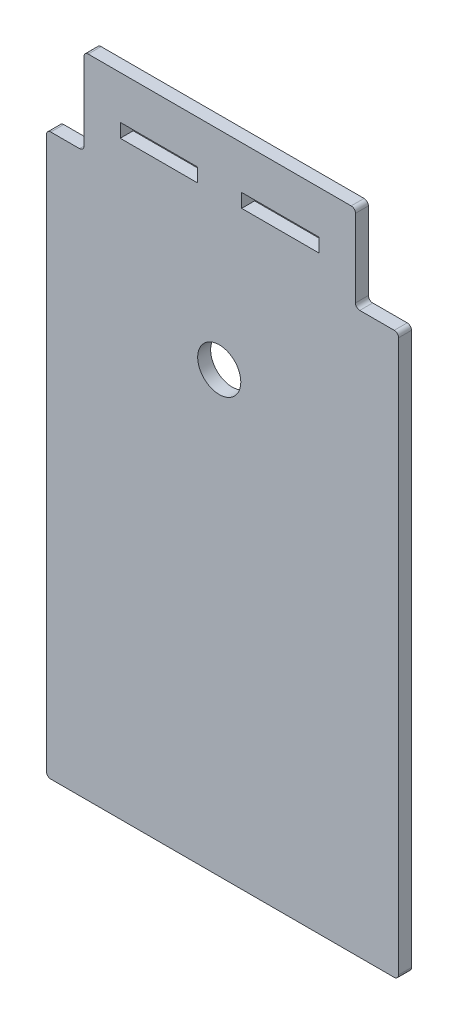
SolidWorks part; units mm, degrees
ref_plane "Alzado" through (0, 0, 0) normal (0, 0, 1) x (1, 0, 0)
ref_plane "Planta" through (0, 0, 0) normal (0, 1, 0) x (1, 0, 0)
ref_plane "Vista lateral" through (0, 0, 0) normal (1, 0, 0) x (0, 0, -1)
sketch "Model" plane through (0, 0, 0) normal (0, 0, 1) x (1, 0, 0)
  line L0 (127.4, 45) -> (109.4364, 45)
  line L1 (127.4, 41.8) -> (127.4, 45)
  line L2 (109.4364, 41.8) -> (127.4, 41.8)
  line L3 (109.4364, 45) -> (109.4364, 41.8)
  line L4 (81.2728, 41.8) -> (99.2364, 41.8)
  line L5 (81.2728, 45) -> (81.2728, 41.8)
  line L6 (99.2364, 45) -> (81.2728, 45)
  line L7 (99.2364, 41.8) -> (99.2364, 45)
  line L8 (64.1636, -39.6154) -> (64.1636, -4)
  line L9 (64.1636, 15.5) -> (64.1636, -4)
  line L10 (64.1636, 34) -> (64.1636, 15.5)
  line L11 (71.8364, 35) -> (65.1636, 35)
  line L12 (72.8364, 54) -> (72.8364, 36)
  line L13 (134.8364, 55) -> (73.8364, 55)
  line L14 (135.8364, 36) -> (135.8364, 54)
  line L15 (144.8364, 35) -> (136.8364, 35)
  line L16 (145.8364, -94) -> (145.8364, 34)
  line L17 (65.1636, -95) -> (144.8364, -95)
  line L18 (64.1636, -39.6154) -> (64.1636, -94)
  arc A0 (65.1636, 35) -> (64.1636, 34) centre (65.1636, 34) ccw
  arc A1 (71.8364, 35) -> (72.8364, 36) centre (71.8364, 36) ccw
  arc A2 (73.8364, 55) -> (72.8364, 54) centre (73.8364, 54) ccw
  arc A3 (135.8364, 54) -> (134.8364, 55) centre (134.8364, 54) ccw
  arc A4 (135.8364, 36) -> (136.8364, 35) centre (136.8364, 36) ccw
  arc A5 (145.8364, 34) -> (144.8364, 35) centre (144.8364, 34) ccw
  arc A6 (144.8364, -95) -> (145.8364, -94) centre (144.8364, -94) ccw
  arc A7 (64.1636, -94) -> (65.1636, -95) centre (65.1636, -94) ccw
  circle A8 centre (104.2364, 6.8) radius 5
extrude "Saliente-Extruir1" add sketch "Model" along normal blind 3
